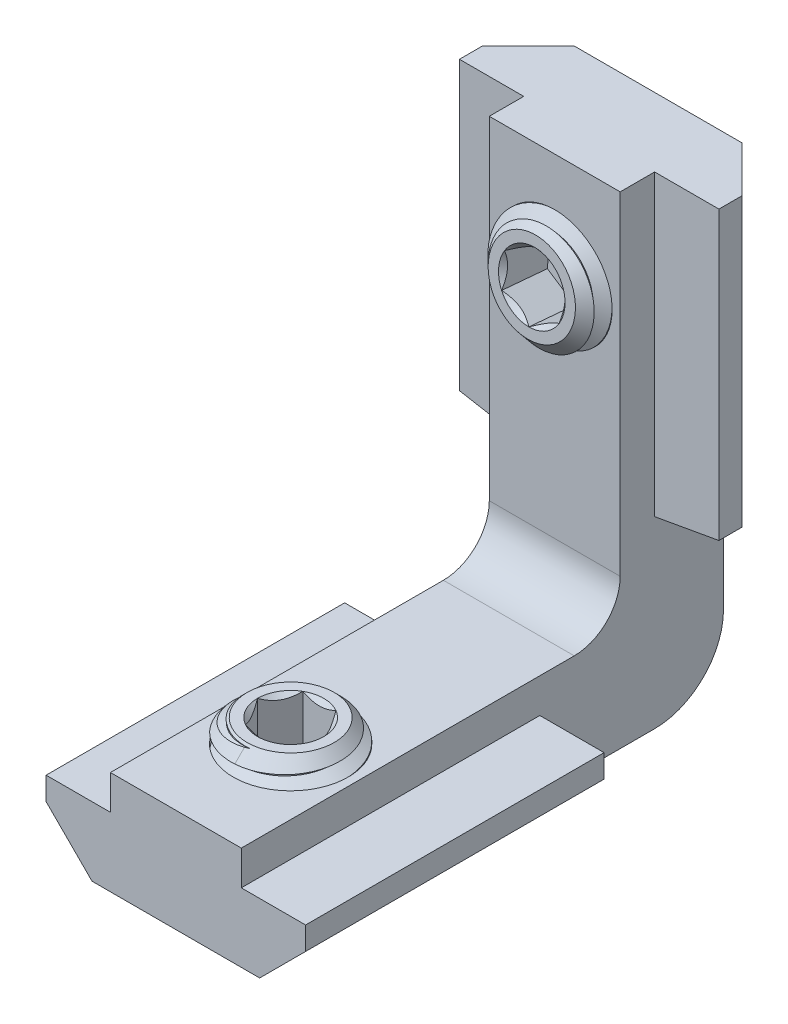
SolidWorks part; units mm, degrees
ref_plane "Front Plane" through (0, 0, 0) normal (0, 0, 1) x (1, 0, 0)
ref_plane "Top Plane" through (0, 0, 0) normal (0, 1, 0) x (1, 0, 0)
ref_plane "Right Plane" through (0, 0, 0) normal (1, 0, 0) x (0, 0, -1)
sketch "Sketch0" plane through (0, 0, 0) normal (1, 0, 0) x (0, 0, -1)
  line L0 (-21, 0) -> (0, 0) construction
  line L1 (0, 0) -> (0, 21) construction
  dimension "D1" = 21
  dimension "D2" = 21
ref_plane "Plane1" through (0, 0, 21) normal (0, 0, 1) x (1, 0, 0)
sketch "Sketch1" plane through (0, 0, 21) normal (0, 0, 1) x (1, 0, 0)
  line L0 (0, 4.5) -> (0, 0) construction
  line L2 (-2.85, 4.5) -> (2.85, 4.5)
  line L3 (-3.65, 0) -> (3.65, 0)
  line L4 (-3.65, 0) -> (-5.65, 2)
  line L5 (-5.65, 2) -> (-5.65, 3)
  line L6 (-5.65, 3) -> (-2.85, 3)
  line L7 (-2.85, 3) -> (-2.85, 4.5)
  line L8 (2.85, 3) -> (2.85, 4.5)
  line L9 (5.65, 3) -> (2.85, 3)
  line L10 (5.65, 2) -> (5.65, 3)
  line L11 (3.65, 0) -> (5.65, 2)
  dimension "D3" = 1
  dimension "D1" = 11.3
  dimension "D2" = 3
  dimension "D4" = 5.7
  dimension "D5" = 4.5
  dimension "D7" = 45
extrude "Boss-Extrude1" add sketch "Sketch1" against normal blind 13
sketch "Sketch2" plane through (0, 4.5, 0) normal (0, 1, 0) x (1, 0, 0)
  line L0 (0, -21) -> (0, 0) construction
  circle A0 centre (0, -16) radius 2.5
  dimension "D1" = 5
  dimension "D2" = 5
extrude "Cut-Extrude1" cut sketch "Sketch2" against normal through all
ref_plane "Plane2" through (0, 21, 0) normal (0, 1, 0) x (-1, 0, 0)
sketch "Sketch3" plane through (0, 21, 0) normal (0, 1, 0) x (-1, 0, 0)
  line L0 (2.85, 4.5) -> (-2.85, 4.5)
  line L1 (0, 4.5) -> (0, 0) construction
  line L2 (2.85, 4.5) -> (2.85, 3)
  line L3 (2.85, 3) -> (5.65, 3)
  line L4 (5.65, 3) -> (5.65, 2)
  line L5 (5.65, 2) -> (3.65, 0)
  line L6 (3.65, 0) -> (-3.65, 0)
  line L7 (-5.65, 2) -> (-3.65, 0)
  line L8 (-5.65, 3) -> (-5.65, 2)
  line L9 (-2.85, 3) -> (-5.65, 3)
  line L10 (-2.85, 4.5) -> (-2.85, 3)
  dimension "D1" = 11.3
  dimension "D2" = 5.7
  dimension "D3" = 4.5
  dimension "D4" = 3
  dimension "D5" = 1
  dimension "D6" = 45
extrude "Boss-Extrude2" add sketch "Sketch3" against normal blind 13 separate body
sketch "Sketch5" plane through (0, 0, 0) normal (1, 0, 0) x (0, 0, -1)
  line L0 (-6.0404, 16.5285) -> (1.8593, 15.8373) construction
  line L1 (-4.7179, 16.4128) -> (0.2179, 15.9809)
  line L2 (-4.7179, 16.4128) -> (-4.5, 18.9032)
  line L3 (0.2179, 15.9809) -> (0.4358, 18.4714)
  line L4 (-4.5, 18.9032) -> (0.4358, 18.4714)
  line L5 (-4.9358, 13.9223) -> (0, 13.4905) construction
  line L6 (0, 8) -> (0, 21) construction
  line L8 (0, 21) -> (0, 16) construction
  line L9 (-4.5, 21) -> (0, 21) construction
  line L10 (-4.5, 8) -> (-4.5, 21) construction
  dimension "D1" = 5
  dimension "D2" = 5
  dimension "D3" = 5
revolve "Cut-Revolve1" cut sketch "Sketch5" angle 360 about L0
sketch "Sketch6" plane through (0, 0, 4.5) normal (0, 0, 1) x (1, 0, 0)
  line L0 (-5.65, 8) -> (-5.65, 8.5)
  line L1 (-5.65, 8) -> (-5.65, 21) construction
  line L2 (-5.65, 8.5) -> (-2.85, 8)
  line L3 (-2.85, 8) -> (-5.65, 8)
  line L4 (0, 0) -> (0, 8) construction
  line L5 (-2.85, 8) -> (2.85, 8) construction
  line L6 (2.85, 8) -> (5.65, 8)
  line L7 (5.65, 8.5) -> (2.85, 8)
  line L8 (5.65, 8) -> (5.65, 8.5)
  dimension "D1" = 0.5
extrude "Cut-Extrude2" cut sketch "Sketch6" against normal through all
sketch "Sketch7" plane through (0, 0, 0) normal (1, 0, 0) x (0, 0, -1)
  line L0 (-8, 0) -> (-3, 0)
  line L1 (0, 3) -> (0, 8)
  line L2 (-8, 4.5) -> (-6.5, 4.5)
  line L3 (-4.5, 6.5) -> (-4.5, 8)
  line L5 (0, 8) -> (-4.5, 8)
  line L6 (-8, 4.5) -> (-8, 0)
  arc A0 (-3, 0) -> (0, 3) centre (-3, 3) ccw
  arc A1 (-6.5, 4.5) -> (-4.5, 6.5) centre (-6.5, 6.5) ccw
  dimension "D1" = 3
  dimension "D2" = 2
extrude "Boss-Extrude3" add sketch "Sketch7" along normal up to vertex (2.85 mm away) and the other way up to vertex (2.85 mm away) up to point (2.85, 4.5, 8) other way up to point (-2.85, 4.5, 8)
sketch "Sketch8" plane through (0, 0, 0) normal (1, 0, 0) x (0, 0, -1)
  line L0 (-16, 10.889) -> (-16, 8.5986) construction
  line L1 (-6.5, 4.5) -> (-21, 4.5) construction
  line L2 (-16, 5.5) -> (-18.5, 5.5)
  line L3 (-16, 5.5) -> (-16, 0.5)
  line L4 (-16, 0.5) -> (-17.75, 0.5)
  line L5 (-18.5, 5.5) -> (-18.5, 1.25)
  line L6 (-18.5, 1.25) -> (-17.75, 0.5)
  dimension "D1" = 5
  dimension "D3" = 1
  dimension "D2" = 5
  dimension "D4" = 3.5
  dimension "D5" = 45
revolve "Revolve1" add sketch "Sketch8" angle 360 about L0
sketch "Sketch9" plane through (0, 5.5, 0) normal (0, 1, 0) x (1, 0, 0)
  circle A1 centre (0, -16) radius 2.5
  circle A2 centre (0, -16) radius 2.5
  point P0 (0, -13.5)
  dimension "D1" = 0
curve "Helix/Spiral1" pitch 0.8 height 5.8 turns 7.25
sketch "Sketch10" plane through (0, 0, 0) normal (1, 0, 0) x (0, 0, -1)
  line L0 (-13.4134, 6.25) -> (-13.4134, 5.45) construction
  line L1 (-13.4134, 5.45) -> (-14.1062, 5.85) construction
  line L2 (-14.1062, 5.85) -> (-13.4134, 6.25) construction
  line L3 (-14.0196, 5.9) -> (-14.0196, 5.8) construction
  line L4 (-13.5, 6.2) -> (-13.5, 5.5) construction
  line L5 (-14.1062, 5.85) -> (-14.0196, 5.85) construction
  line L6 (-13.5, 5.85) -> (-13.4134, 5.85) construction
  line L7 (-14.0196, 5.9) -> (-14.0196, 5.8)
  line L8 (-14.0196, 5.8) -> (-13.4567, 5.475)
  line L9 (-13.4567, 5.475) -> (-13.4567, 6.225)
  line L10 (-13.4567, 6.225) -> (-14.0196, 5.9)
  point P15 (-13.4567, 5.85)
  dimension "D1" = 0.8
  dimension "D2" = 0.1
sweep "Cut-Sweep1" cut profiles "Sketch10" path "Helix/Spiral1"
sketch "Sketch11" plane through (0, 5.5, 0) normal (0, 1, 0) x (1, 0, 0)
  circle A0 centre (0, -16) radius 1.8938
extrude "Cut-Extrude3" cut sketch "Sketch11" against normal through all draft 45 flip side to cut
sketch "Sketch12" plane through (0, 5.5, 0) normal (0, 1, 0) x (1, 0, 0)
  line L1 (1.4434, -16) -> (0.7217, -14.75)
  line L2 (0.7217, -14.75) -> (-0.7217, -14.75)
  line L3 (-0.7217, -14.75) -> (-1.4434, -16)
  line L4 (-1.4434, -16) -> (-0.7217, -17.25)
  line L5 (-0.7217, -17.25) -> (0.7217, -17.25)
  line L6 (0.7217, -17.25) -> (1.4434, -16)
  circle A0 centre (0, -16) radius 1.25 construction
  dimension "D1" = 2.5
extrude "Cut-Extrude4" cut sketch "Sketch12" against normal blind 2
sketch "Sketch13" plane through (0, 5.5, 0) normal (0, 1, 0) x (1, 0, 0)
  circle A0 centre (0, -16) radius 1.4434
extrude "Cut-Extrude5" cut sketch "Sketch13" against normal through all draft 45
sketch "Sketch14" plane through (0, 0, 0) normal (1, 0, 0) x (0, 0, -1)
  line L1 (-10.9711, 16.9598) -> (6.6853, 15.4151) construction
  line L2 (-1.0483, 18.6013) -> (-0.3665, 17.7887)
  line L3 (-5.5, 16.4812) -> (-0.519, 16.0454)
  line L4 (-5.5, 16.4812) -> (-5.2821, 18.9717)
  line L5 (-0.519, 16.0454) -> (-0.3665, 17.7887)
  line L6 (-5.2821, 18.9717) -> (-1.0483, 18.6013)
  line L7 (-4.7179, 16.4128) -> (0.2179, 15.9809) construction
  line L8 (-4.5, 21) -> (-4.5, 6.5) construction
  dimension "D1" = 5
  dimension "D2" = 5
  dimension "D3" = 3.5
  dimension "D4" = 45
  dimension "D5" = 1
revolve "Revolve2" add sketch "Sketch14" angle 360 about L1
sketch "Sketch15" plane through (0, 0.6027, 6.8892) normal (0, 0.0872, 0.9962) x (1, 0, 0)
  circle A1 centre (0, 15.9391) radius 2.5
  circle A2 centre (0, 15.9391) radius 2.5
  point P0 (0, 18.4391)
  dimension "D1" = 0
curve "Helix/Spiral2" pitch 0.8 height 5.8 turns 7.25
sketch "Sketch16" plane through (0, 0, 0) normal (1, 0, 0) x (0, 0, -1)
  line L0 (-6.0217, 19.1233) -> (-5.2248, 19.0536) construction
  line L1 (-5.2248, 19.0536) -> (-5.6836, 18.3983) construction
  line L2 (-5.6836, 18.3983) -> (-6.0217, 19.1233) construction
  line L3 (-1.0483, 18.6013) -> (-5.2821, 18.9717) construction
  line L4 (-5.6232, 19.0885) -> (-5.6308, 19.0022) construction
  line L5 (-5.7259, 18.4889) -> (-5.6263, 18.4802) construction
  line L6 (-5.6308, 19.0022) -> (-5.6761, 18.4845) construction
  line L7 (-5.6761, 18.4845) -> (-5.6836, 18.3983) construction
  line L8 (-5.9794, 19.0327) -> (-5.2821, 18.9717) construction
  line L9 (-6.0006, 19.078) -> (-5.7259, 18.4889)
  line L10 (-5.7259, 18.4889) -> (-5.6263, 18.4802)
  line L11 (-5.6263, 18.4802) -> (-5.2534, 19.0126)
  line L12 (-5.2534, 19.0126) -> (-6.0006, 19.078)
  point P13 (-5.627, 19.0453)
  dimension "D1" = 0.8
  dimension "D2" = 0.1
sweep "Cut-Sweep2" cut profiles "Sketch16" path "Helix/Spiral2"
sketch "Sketch17" plane through (0, 0.6027, 6.8892) normal (0, 0.0872, 0.9962) x (1, 0, 0)
  circle A0 centre (0, 15.9391) radius 1.8938
extrude "Cut-Extrude6" cut sketch "Sketch17" against normal through all draft 45 flip side to cut
sketch "Sketch18" plane through (0, 0.6027, 6.8892) normal (0, 0.0872, 0.9962) x (1, 0, 0)
  line L1 (0, 17.3825) -> (-1.25, 16.6608)
  line L2 (-1.25, 16.6608) -> (-1.25, 15.2174)
  line L3 (-1.25, 15.2174) -> (0, 14.4957)
  line L4 (0, 14.4957) -> (1.25, 15.2174)
  line L5 (1.25, 15.2174) -> (1.25, 16.6608)
  line L6 (1.25, 16.6608) -> (0, 17.3825)
  circle A0 centre (0, 15.9391) radius 1.25 construction
  dimension "D1" = 2.5
extrude "Cut-Extrude7" cut sketch "Sketch18" against normal blind 2
sketch "Sketch19" plane through (0, 0.6027, 6.8892) normal (0, 0.0872, 0.9962) x (1, 0, 0)
  circle A0 centre (0, 15.9391) radius 1.4434
extrude "Cut-Extrude8" cut sketch "Sketch19" against normal through all draft 45
equation "\"D3@Helix/Spiral1\" = \"D4@Helix/Spiral1\" + \"D2@Sketch8\""
equation "\"D1@Sketch10\" = \"D4@Helix/Spiral1\""
equation "\"D2@Sketch10\" = \"D1@Sketch10\" / 8"
equation "\"D3@Helix/Spiral2\" = \"D4@Helix/Spiral2\" + \"D2@Sketch14\""
equation "\"D1@Sketch16\" = \"D4@Helix/Spiral2\""
equation "\"D2@Sketch16\" = \"D1@Sketch16\" / 8"
